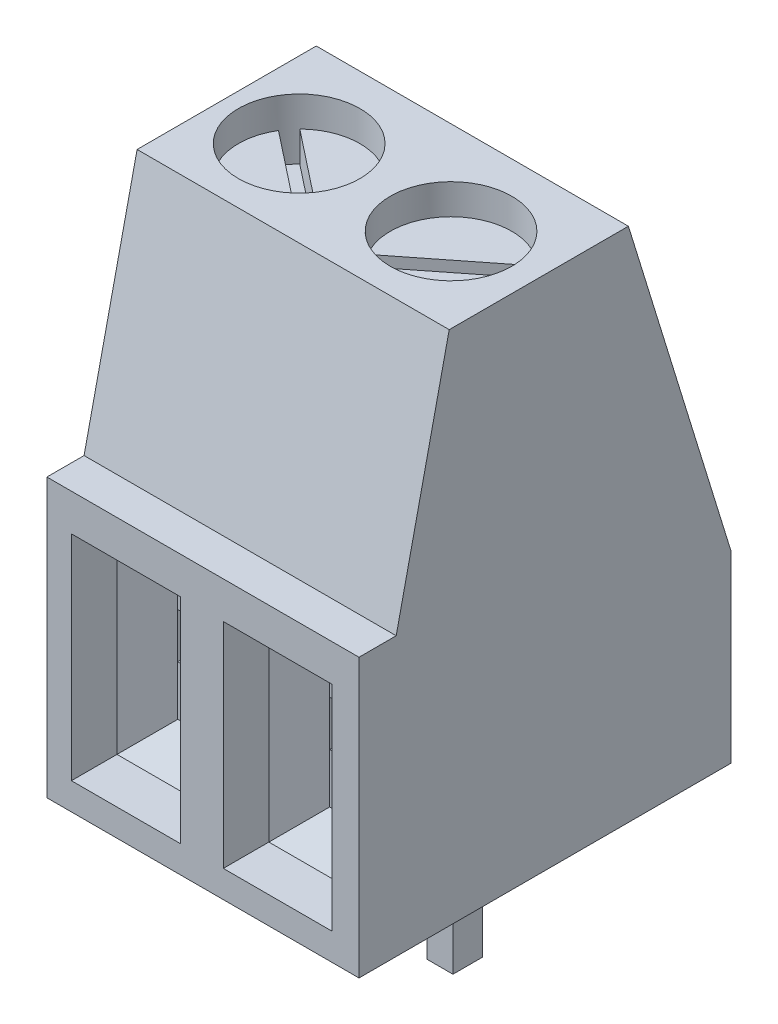
SolidWorks part; units mm, degrees
ref_plane "Front Plane" through (0, 0, 0) normal (0, 0, 1) x (1, 0, 0)
ref_plane "Top Plane" through (0, 0, 0) normal (0, 1, 0) x (1, 0, 0)
ref_plane "Right Plane" through (0, 0, 0) normal (1, 0, 0) x (0, 0, -1)
sketch "Sketch1" plane through (0, 0, 0) normal (0, 1, 0) x (1, 0, 0)
  line L1 (0, 0) -> (20.701, 0)
  line L2 (0, 0) -> (0, 6.223)
  line L3 (0, 6.223) -> (20.701, 6.223)
  line L4 (20.701, 0) -> (20.701, 6.223)
  dimension "D1" = 20.701
  dimension "D2" = 6.223
extrude "Extrude1" add sketch "Sketch1" along normal blind 8.636
sketch "Sketch2" plane through (20.701, 0, 0) normal (1, 0, 0) x (0, 0, -1)
  line L0 (-2.8691, 4.6459) -> (0.6218, 4.6459)
  line L1 (0.6218, 4.6459) -> (2.2176, 11.8272)
  line L2 (2.2176, 11.8272) -> (-2.8691, 11.8272)
  line L3 (-2.8691, 11.8272) -> (-2.8691, 4.6459)
extrude "Cut-Extrude1" cut sketch "Sketch2" against normal blind 25.4
sketch "Sketch3" plane through (20.701, 0, 0) normal (1, 0, 0) x (0, 0, -1)
  line L0 (4.013, 10.2314) -> (6.9054, 0.8558)
  line L1 (6.9054, 0.8558) -> (9.1994, 0.8558)
  line L2 (9.1994, 0.8558) -> (9.1994, 10.2314)
  line L3 (9.1994, 10.2314) -> (4.013, 10.2314)
extrude "Cut-Extrude2" cut sketch "Sketch3" against normal blind 25.4
sketch "Sketch4" plane through (0, 8.636, 0) normal (0, 1, 0) x (1, 0, 0)
  line L0 (0, 4.5051) -> (0, 1.5085) construction
  circle A0 centre (1.27, 2.9491) radius 1.016
  circle A1 centre (3.81, 2.9491) radius 1.016
  circle A2 centre (6.35, 2.9491) radius 1.016
  circle A3 centre (8.89, 2.9491) radius 1.016
  circle A4 centre (11.43, 2.9491) radius 1.016
  circle A5 centre (13.97, 2.9491) radius 1.016
  circle A6 centre (16.51, 2.9491) radius 1.016
  circle A7 centre (19.05, 2.9491) radius 1.016
  dimension "D1" = 1.27
extrude "Cut-Extrude3" cut sketch "Sketch4" against normal blind 0.508
sketch "Sketch5" plane through (0, 8.128, 0) normal (0, 1, 0) x (1, 0, 0)
  line L8 (18.1734, 3.4782) -> (19.7694, 2.2205)
  line L9 (16.7061, 3.9541) -> (16.0726, 2.0233)
  line L10 (12.9692, 3.1653) -> (14.8868, 2.4932)
  line L11 (11.303, 3.9651) -> (11.303, 1.9331)
  line L12 (8.6939, 1.9441) -> (9.3274, 3.8749)
  line L13 (5.334, 2.8221) -> (7.366, 2.8221)
  line L14 (3.0906, 2.2205) -> (4.6866, 3.4782)
  line L15 (0.3934, 3.4782) -> (1.9894, 2.2205)
  line L16 (18.3306, 3.6777) -> (19.9266, 2.42)
  line L17 (16.9474, 3.8749) -> (16.3139, 1.9441)
  line L18 (13.0532, 3.405) -> (14.9708, 2.7329)
  line L19 (11.557, 3.9651) -> (11.557, 1.9331)
  line L20 (8.4526, 2.0233) -> (9.0861, 3.9541)
  line L21 (5.334, 3.0761) -> (7.366, 3.0761)
  line L22 (2.9334, 2.42) -> (4.5294, 3.6777)
  line L23 (0.5506, 3.6777) -> (2.1466, 2.42)
  circle A13 centre (1.27, 2.9491) radius 1.016
  circle A14 centre (3.81, 2.9491) radius 1.016
  circle A15 centre (6.35, 2.9491) radius 1.016
  circle A16 centre (8.89, 2.9491) radius 1.005
  circle A17 centre (11.43, 2.9491) radius 1.016
  circle A18 centre (13.97, 2.9491) radius 1.016
  circle A19 centre (16.51, 2.9491) radius 1.016
  circle A20 centre (19.05, 2.9491) radius 0.9996
  circle M1 centre (1.27, 2.9491) radius 1.016
extrude "Cut-Extrude4" cut sketch "Sketch5" against normal blind 0.508 contours L23 L15 M1 | L14 A14 L22 | L13 A15 L21 | L12 A16 L20 | L19 A17 L11 | L10 A18 L18 | L17 A19 L9 | L8 A20 L16
sketch "Sketch6" plane through (0, 0, 0) normal (0, 0, 1) x (1, 0, 0)
  line L0 (2.9501, 4.0288) -> (2.9501, 0.4524)
  line L1 (0.4101, 4.0288) -> (2.232, 4.0288)
  line L2 (0.4101, 4.0288) -> (0.4101, 0.4524)
  line L3 (0.4101, 0.4524) -> (2.232, 0.4524)
  line L4 (2.232, 4.0288) -> (2.232, 0.4524)
  line L5 (2.9501, 4.0288) -> (4.772, 4.0288)
  line L6 (4.772, 4.0288) -> (4.772, 0.4524)
  line L7 (2.9501, 0.4524) -> (4.772, 0.4524)
  line L8 (5.4901, 4.0288) -> (5.4901, 0.4524)
  line L9 (5.4901, 4.0288) -> (7.312, 4.0288)
  line L10 (7.312, 4.0288) -> (7.312, 0.4524)
  line L11 (5.4901, 0.4524) -> (7.312, 0.4524)
  line L12 (8.0301, 4.0288) -> (8.0301, 0.4524)
  line L13 (8.0301, 4.0288) -> (9.852, 4.0288)
  line L14 (9.852, 4.0288) -> (9.852, 0.4524)
  line L15 (8.0301, 0.4524) -> (9.852, 0.4524)
  line L16 (10.5701, 4.0288) -> (10.5701, 0.4524)
  line L17 (10.5701, 4.0288) -> (12.392, 4.0288)
  line L18 (12.392, 4.0288) -> (12.392, 0.4524)
  line L19 (10.5701, 0.4524) -> (12.392, 0.4524)
  line L20 (13.1101, 4.0288) -> (13.1101, 0.4524)
  line L21 (13.1101, 4.0288) -> (14.932, 4.0288)
  line L22 (14.932, 4.0288) -> (14.932, 0.4524)
  line L23 (13.1101, 0.4524) -> (14.932, 0.4524)
  line L24 (15.6501, 4.0288) -> (15.6501, 0.4524)
  line L25 (15.6501, 4.0288) -> (17.472, 4.0288)
  line L26 (17.472, 4.0288) -> (17.472, 0.4524)
  line L27 (15.6501, 0.4524) -> (17.472, 0.4524)
  line L28 (18.1901, 4.0288) -> (18.1901, 0.4524)
  line L29 (18.1901, 4.0288) -> (20.012, 4.0288)
  line L30 (20.012, 4.0288) -> (20.012, 0.4524)
  line L31 (18.1901, 0.4524) -> (20.012, 0.4524)
extrude "Cut-Extrude5" cut sketch "Sketch6" against normal blind 1.27
chamfer "Chamfer1" distance 0.508 angle 45 8 edges at (4.772, 2.2406, -1.27) (3.8611, 0.4524, -1.27) (2.9501, 2.2406, -1.27) (3.8611, 4.0288, -1.27) (1.3211, 4.0288, -1.27) (2.232, 2.2406, -1.27) (1.3211, 0.4524, -1.27) (0.4101, 2.2406, -1.27)
sketch "Sketch7" plane through (0, 0, -1.27) normal (0, 0, 1) x (1, 0, 0)
  line L0 (0.9181, 3.5208) -> (0.9181, 0.9604) construction
  line L1 (0.9181, 2.5517) -> (1.724, 2.5517)
  line L2 (0.9181, 2.5517) -> (0.9181, 1.7937)
  line L3 (0.9181, 1.7937) -> (1.724, 1.7937)
  line L4 (1.724, 2.5517) -> (1.724, 1.7937)
  line L5 (1.724, 0.9604) -> (1.724, 3.5208) construction
  line L6 (3.4581, 2.5517) -> (3.4581, 1.7937)
  line L7 (3.4581, 2.5517) -> (4.264, 2.5517)
  line L8 (4.264, 2.5517) -> (4.264, 1.7937)
  line L9 (3.4581, 1.7937) -> (4.264, 1.7937)
  line L10 (5.9981, 2.5517) -> (5.9981, 1.7937)
  line L11 (5.9981, 2.5517) -> (6.804, 2.5517)
  line L12 (6.804, 2.5517) -> (6.804, 1.7937)
  line L13 (5.9981, 1.7937) -> (6.804, 1.7937)
  line L14 (8.5381, 2.5517) -> (8.5381, 1.7937)
  line L15 (8.5381, 2.5517) -> (9.344, 2.5517)
  line L16 (9.344, 2.5517) -> (9.344, 1.7937)
  line L17 (8.5381, 1.7937) -> (9.344, 1.7937)
  line L18 (11.0781, 2.5517) -> (11.0781, 1.7937)
  line L19 (11.0781, 2.5517) -> (11.884, 2.5517)
  line L20 (11.884, 2.5517) -> (11.884, 1.7937)
  line L21 (11.0781, 1.7937) -> (11.884, 1.7937)
  line L22 (13.6181, 2.5517) -> (13.6181, 1.7937)
  line L23 (13.6181, 2.5517) -> (14.424, 2.5517)
  line L24 (14.424, 2.5517) -> (14.424, 1.7937)
  line L25 (13.6181, 1.7937) -> (14.424, 1.7937)
  line L26 (16.1581, 2.5517) -> (16.1581, 1.7937)
  line L27 (16.1581, 2.5517) -> (16.964, 2.5517)
  line L28 (16.964, 2.5517) -> (16.964, 1.7937)
  line L29 (16.1581, 1.7937) -> (16.964, 1.7937)
  line L30 (18.6981, 2.5517) -> (18.6981, 1.7937)
  line L31 (18.6981, 2.5517) -> (19.504, 2.5517)
  line L32 (19.504, 2.5517) -> (19.504, 1.7937)
  line L33 (18.6981, 1.7937) -> (19.504, 1.7937)
extrude "Cut-Extrude6" cut sketch "Sketch7" against normal blind 1.27
sketch "Sketch8" plane through (0, 0, 0) normal (0, -1, 0) x (1, 0, 0)
  line L0 (3.6128, -2.7447) -> (3.6128, -3.2358)
  line L1 (1.0728, -2.7447) -> (1.5062, -2.7447)
  line L2 (1.0728, -2.7447) -> (1.0728, -3.2358)
  line L3 (1.0728, -3.2358) -> (1.5062, -3.2358)
  line L4 (1.5062, -2.7447) -> (1.5062, -3.2358)
  line L5 (3.6128, -2.7447) -> (4.0462, -2.7447)
  line L6 (4.0462, -2.7447) -> (4.0462, -3.2358)
  line L7 (3.6128, -3.2358) -> (4.0462, -3.2358)
  line L8 (6.1528, -2.7447) -> (6.1528, -3.2358)
  line L9 (6.1528, -2.7447) -> (6.5862, -2.7447)
  line L10 (6.5862, -2.7447) -> (6.5862, -3.2358)
  line L11 (6.1528, -3.2358) -> (6.5862, -3.2358)
  line L12 (8.6928, -2.7447) -> (8.6928, -3.2358)
  line L13 (8.6928, -2.7447) -> (9.1262, -2.7447)
  line L14 (9.1262, -2.7447) -> (9.1262, -3.2358)
  line L15 (8.6928, -3.2358) -> (9.1262, -3.2358)
  line L16 (11.2328, -2.7447) -> (11.2328, -3.2358)
  line L17 (11.2328, -2.7447) -> (11.6662, -2.7447)
  line L18 (11.6662, -2.7447) -> (11.6662, -3.2358)
  line L19 (11.2328, -3.2358) -> (11.6662, -3.2358)
  line L20 (13.7728, -2.7447) -> (13.7728, -3.2358)
  line L21 (13.7728, -2.7447) -> (14.2062, -2.7447)
  line L22 (14.2062, -2.7447) -> (14.2062, -3.2358)
  line L23 (13.7728, -3.2358) -> (14.2062, -3.2358)
  line L24 (16.3128, -2.7447) -> (16.3128, -3.2358)
  line L25 (16.3128, -2.7447) -> (16.7462, -2.7447)
  line L26 (16.7462, -2.7447) -> (16.7462, -3.2358)
  line L27 (16.3128, -3.2358) -> (16.7462, -3.2358)
  line L28 (18.8528, -2.7447) -> (18.8528, -3.2358)
  line L29 (18.8528, -2.7447) -> (19.2862, -2.7447)
  line L30 (19.2862, -2.7447) -> (19.2862, -3.2358)
  line L31 (18.8528, -3.2358) -> (19.2862, -3.2358)
extrude "Extrude2" add sketch "Sketch8" along normal blind 1.905
sketch "Sketch9" plane through (0, 8.636, 0) normal (0, 1, 0) x (1, 0, 0)
  line L1 (7.5567, 8.0072) -> (21.3925, 8.0072)
  line L2 (7.5567, 8.0072) -> (7.5567, -3.0614)
  line L3 (7.5567, -3.0614) -> (21.3925, -3.0614)
  line L4 (21.3925, 8.0072) -> (21.3925, -3.0614)
extrude "Cut-Extrude7" cut sketch "Sketch9" against normal blind 25.4
sketch "Sketch10" plane through (0, 8.636, 0) normal (0, 1, 0) x (1, 0, 0)
  line L0 (7.5567, 4.5051) -> (7.5567, 1.5085) construction
  line L1 (5.2199, 8.3689) -> (8.6085, 8.3689)
  line L2 (5.2199, 8.3689) -> (5.2199, -2.1459)
  line L3 (5.2199, -2.1459) -> (8.6085, -2.1459)
  line L4 (8.6085, 8.3689) -> (8.6085, -2.1459)
  dimension "D1" = 2.3368
extrude "Cut-Extrude8" cut sketch "Sketch10" against normal blind 25.4
